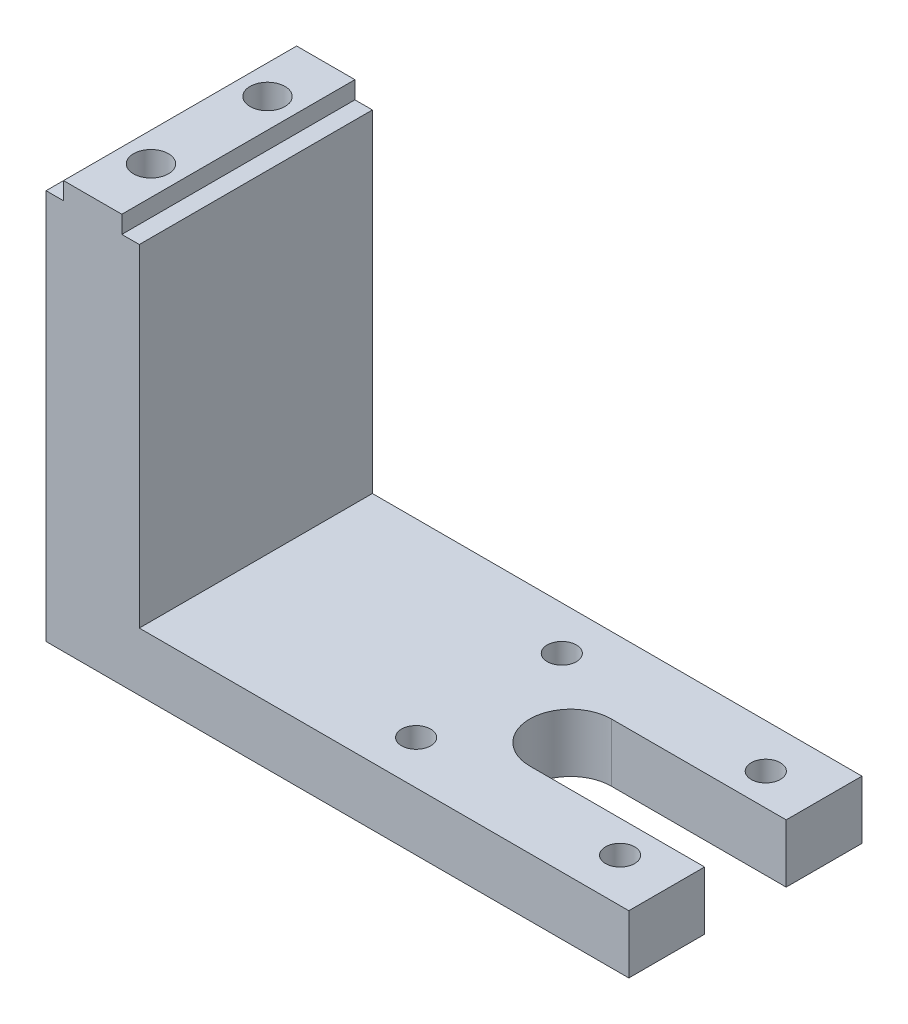
SolidWorks part; units mm, degrees
ref_plane "前基準面" through (0, 0, 0) normal (0, 0, 1) x (1, 0, 0)
ref_plane "上基準面" through (0, 0, 0) normal (0, 1, 0) x (1, 0, 0)
ref_plane "右基準面" through (0, 0, 0) normal (1, 0, 0) x (0, 0, -1)
sketch "草圖1" plane through (0, 0, 0) normal (0, 0, 1) x (1, 0, 0)
  line L0 (0, 0) -> (84, 0)
  line L1 (84, 0) -> (84, -10)
  line L2 (84, -10) -> (-16, -10)
  line L3 (-16, -10) -> (-16, 57)
  line L4 (-16, 57) -> (-13, 57)
  line L5 (-13, 57) -> (-13, 60)
  line L6 (-13, 60) -> (-3, 60)
  line L7 (-3, 60) -> (-3, 57)
  line L8 (-3, 57) -> (0, 57)
  line L9 (0, 57) -> (0, 0)
  dimension "D1" = 100
  dimension "D2" = 10
  dimension "D3" = 67
  dimension "D4" = 10
  dimension "D5" = 16
  dimension "D6" = 3
extrude "填料-伸長1" add sketch "草圖1" along normal mid plane 40
sketch "草圖4" plane through (0, 60, 0) normal (0, 1, 0) x (1, 0, 0)
  line L0 (-8, 16.3639) -> (-8, -20) construction
  line L1 (-3, -20) -> (-13, -20) construction
  line L2 (-24.9762, 0) -> (97.165, 0) construction
  line L3 (-3, -20) -> (-3, 20) construction
  line L4 (-13, -20) -> (-13, 20) construction
  circle A0 centre (-8, 10) radius 3
  circle A1 centre (-8, -10) radius 3
  dimension "D1" = 6
  dimension "D2" = 20
extrude "除料-伸長1" cut sketch "草圖4" against normal blind 10
sketch "草圖5" plane through (0, 0, 0) normal (0, 1, 0) x (1, 0, 0)
  line L0 (84, -20) -> (84, 20) construction
  line L1 (84, 7) -> (54, 7)
  line L2 (84, 7) -> (84, -7)
  line L3 (84, -7) -> (54, -7)
  line L4 (0, -20) -> (0, 20) construction
  line L5 (-19.8994, 0) -> (92.5218, 0) construction
  circle A0 centre (40, -12.5) radius 2.5
  arc A1 (54, -7) -> (54, 7) centre (54, 0) cw
  circle A2 centre (40, 12.5) radius 2.5
  circle A3 centre (75, 12.5) radius 2.5
  circle A4 centre (75, -12.5) radius 2.5
  dimension "D1" = 5
  dimension "D3" = 7
  dimension "D4" = 40
  dimension "D5" = 25
  dimension "D6" = 2
  dimension "D7" = 35
  dimension "D2" = 30
extrude "除料-伸長2" cut sketch "草圖5" against normal through all
